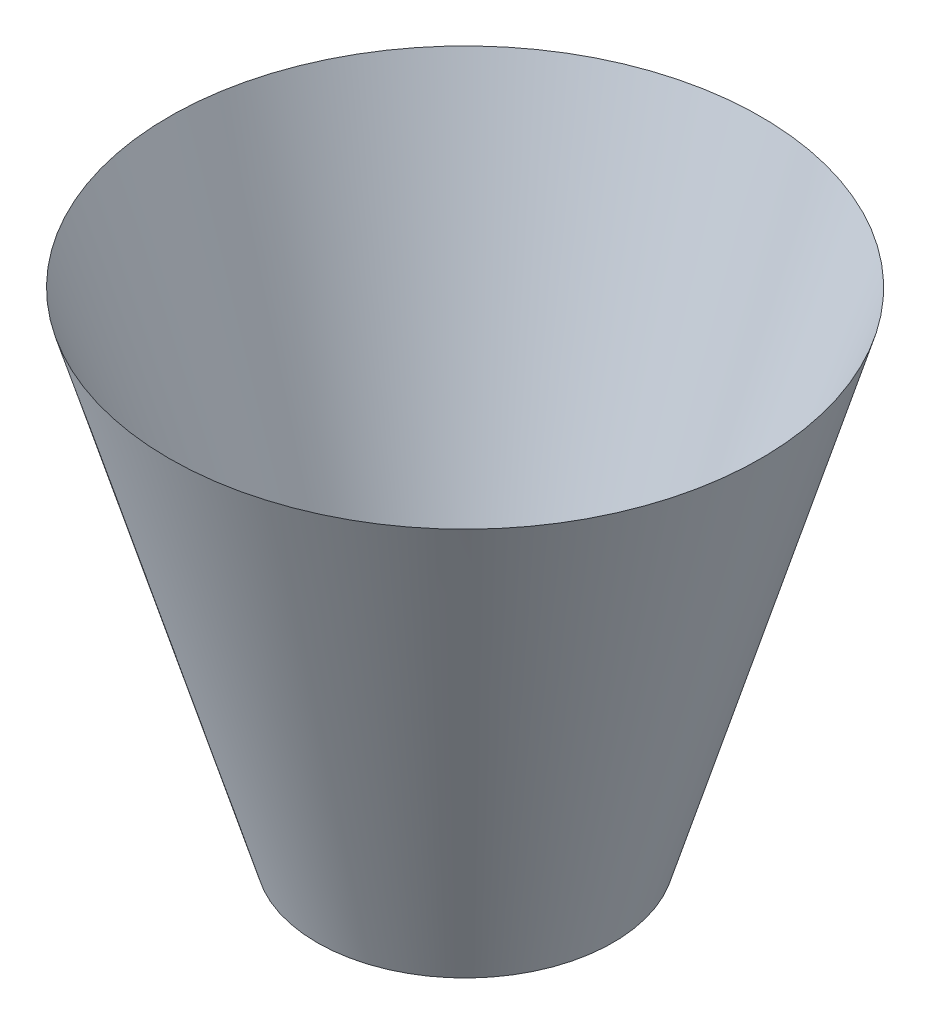
SolidWorks part; units mm, degrees
ref_plane "前视基准面" through (0, 0, 0) normal (0, 0, 1) x (1, 0, 0)
ref_plane "上视基准面" through (0, 0, 0) normal (0, 1, 0) x (1, 0, 0)
ref_plane "右视基准面" through (0, 0, 0) normal (1, 0, 0) x (0, 0, -1)
sketch "草图1" plane through (0, 0, 0) normal (0, 1, 0) x (1, 0, 0)
  circle A0 centre (0, 0) radius 300
  dimension "D1" = 600
ref_plane "基准面4" through (0, 1000, 0) normal (0, 1, 0) x (1, 0, 0)
sketch "草图2" plane through (0, 1000, 0) normal (0, 1, 0) x (1, 0, 0)
  circle A0 centre (0, 0) radius 600
  dimension "D1" = 1200
loft "放样1" add profiles "草图1", "草图2"
sketch "草图3" plane through (0, 0, 0) normal (0, 1, 0) x (1, 0, 0)
  circle A0 centre (0, 0) radius 250
  dimension "D1" = 500
sketch "草图4" plane through (0, 1000, 0) normal (0, 1, 0) x (1, 0, 0)
  circle A0 centre (0, 0) radius 550
  dimension "D1" = 1100
loft "切除-放样1" cut profiles "草图3" section "草图3" section edge at (0, 1000, 600)
